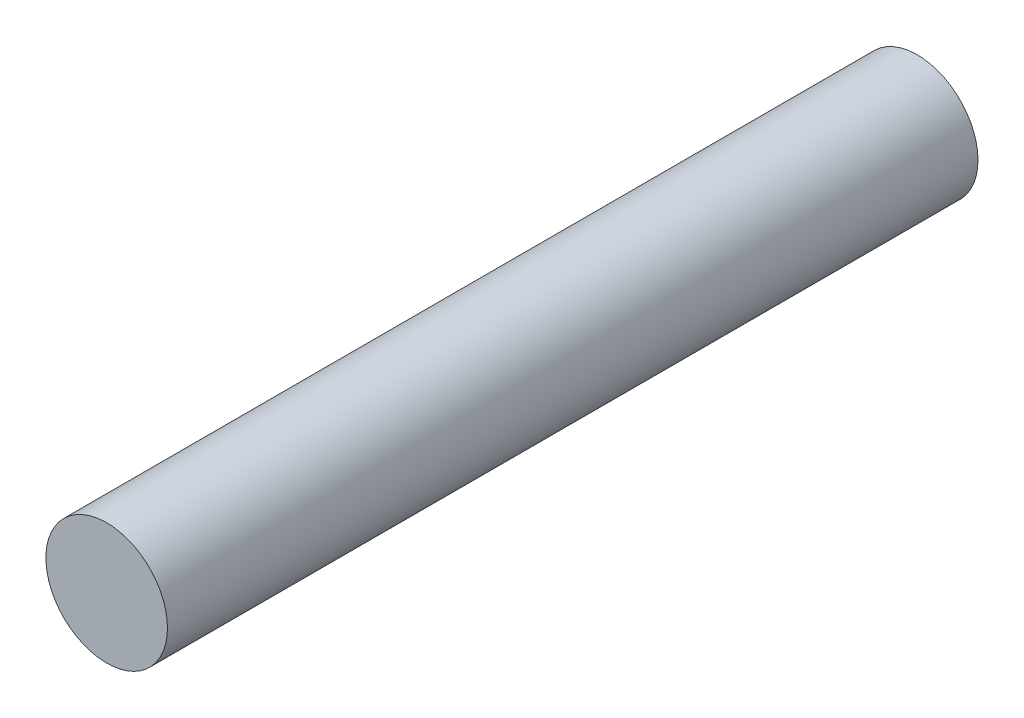
SolidWorks part; units mm, degrees
ref_plane "Front Plane" through (0, 0, 0) normal (0, 0, 1) x (1, 0, 0)
ref_plane "Top Plane" through (0, 0, 0) normal (0, 1, 0) x (1, 0, 0)
ref_plane "Right Plane" through (0, 0, 0) normal (1, 0, 0) x (0, 0, -1)
sketch "Sketch1" plane through (0, 0, 0) normal (0, 0, 1) x (1, 0, 0)
  circle A0 centre (0, 0) radius 4.7625
  dimension "D1" = 9.525
extrude "Boss-Extrude1" add sketch "Sketch1" along normal mid plane 63.5
